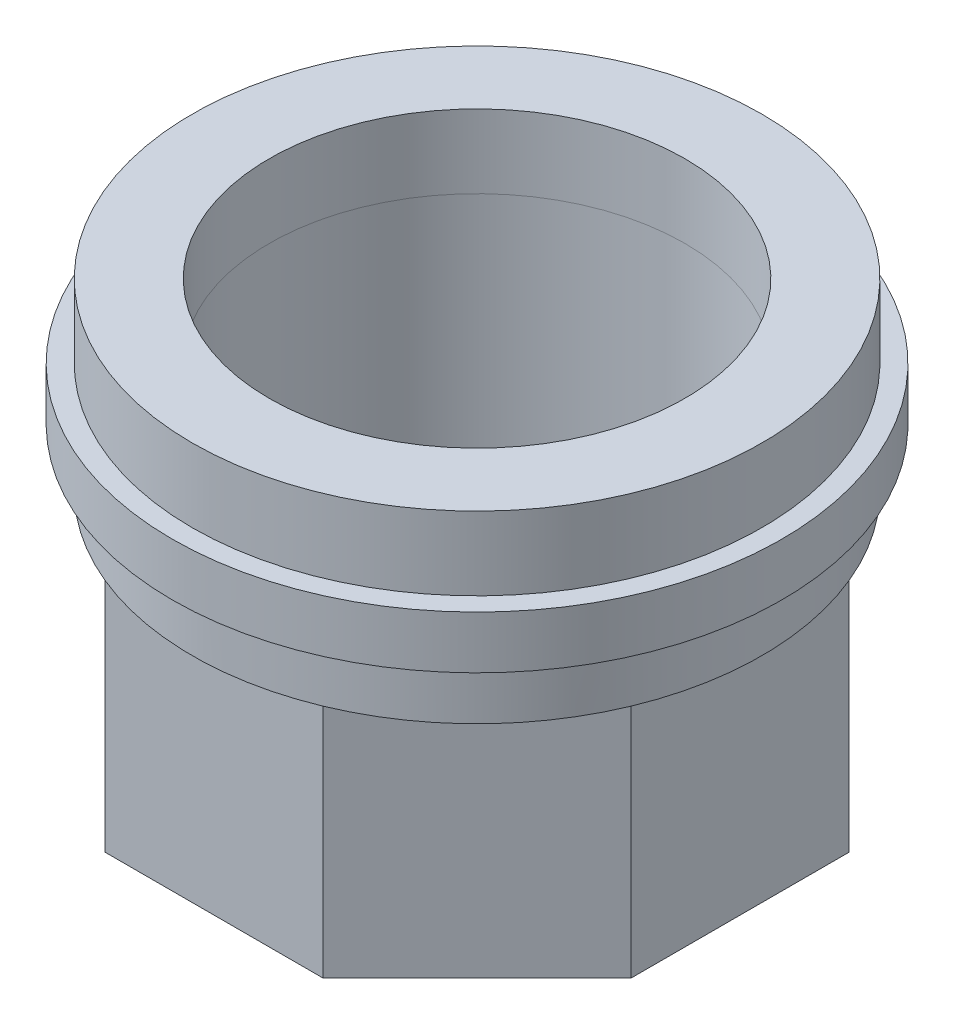
SolidWorks part; units mm, degrees
ref_plane "Plano frontal" through (0, 0, 0) normal (0, 0, 1) x (1, 0, 0)
ref_plane "Plano superior" through (0, 0, 0) normal (0, 1, 0) x (1, 0, 0)
ref_plane "Plano direito" through (0, 0, 0) normal (1, 0, 0) x (0, 0, -1)
sketch "Esboço1" plane through (0, 0, 0) normal (0, 1, 0) x (1, 0, 0)
  line L1 (7.8701, -19) -> (19, -7.8701)
  line L2 (19, -7.8701) -> (19, 7.8701)
  line L3 (19, 7.8701) -> (7.8701, 19)
  line L4 (7.8701, 19) -> (-7.8701, 19)
  line L5 (-7.8701, 19) -> (-19, 7.8701)
  line L6 (-19, 7.8701) -> (-19, -7.8701)
  line L7 (-19, -7.8701) -> (-7.8701, -19)
  line L8 (-7.8701, -19) -> (7.8701, -19)
  circle A0 centre (0, 0) radius 19 construction
  circle A1 centre (0, 0) radius 15
  dimension "D2" = 30
  dimension "D1" = 38
extrude "Ressalto-extrusão1" add sketch "Esboço1" along normal blind 17
sketch "Esboço2" plane through (0, 17, 0) normal (0, 1, 0) x (1, 0, 0)
  circle A0 centre (0, 0) radius 15 construction
  circle A1 centre (0, 0) radius 15
  circle A2 centre (0, 0) radius 20.5655
extrude "Ressalto-extrusão2" add sketch "Esboço2" along normal blind 4.2
sketch "Esboço3" plane through (0, 21.2, 0) normal (0, 1, 0) x (1, 0, 0)
  circle A0 centre (0, 0) radius 15 construction
  circle A1 centre (0, 0) radius 15
  circle A2 centre (0, 0) radius 22
  dimension "D1" = 44
extrude "Ressalto-extrusão3" add sketch "Esboço3" along normal blind 3.8
sketch "Esboço4" plane through (0, 25, 0) normal (0, 1, 0) x (1, 0, 0)
  circle A0 centre (0, 0) radius 20.5655 construction
  circle A1 centre (0, 0) radius 20.5655
  circle A2 centre (0, 0) radius 15 construction
  circle A3 centre (0, 0) radius 15
extrude "Ressalto-extrusão4" add sketch "Esboço4" along normal blind 5.3 separate body
